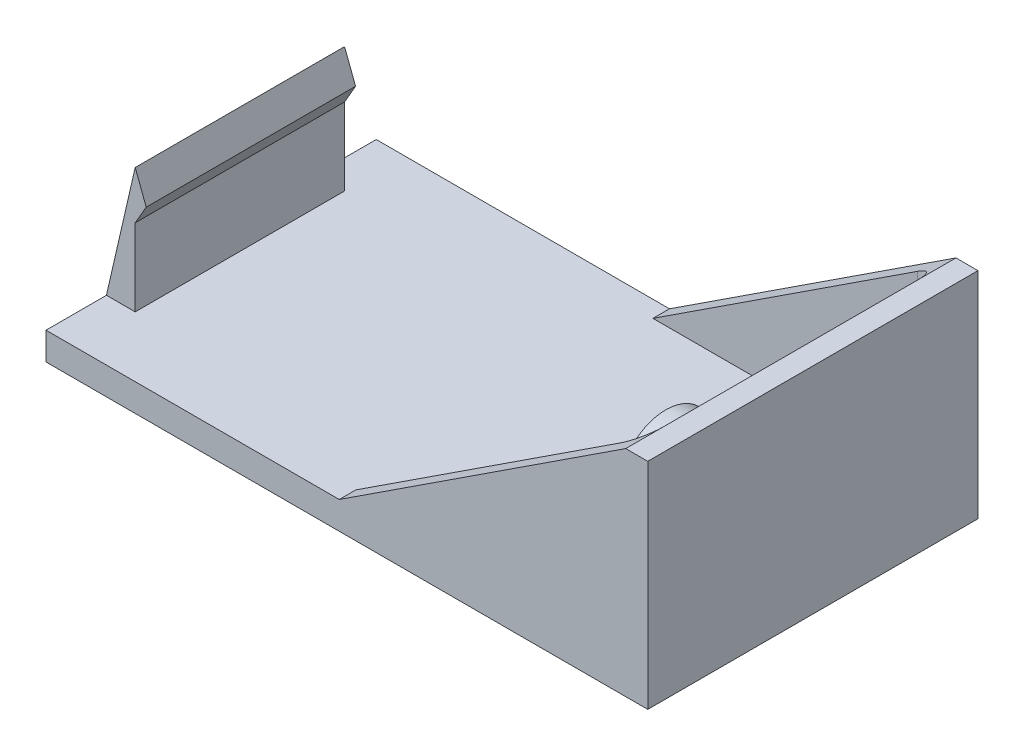
SolidWorks part; units mm, degrees
material "PUR"
ref_plane "Спереди" through (0, 0, 0) normal (0, 0, 1) x (1, 0, 0)
ref_plane "Сверху" through (0, 0, 0) normal (0, 1, 0) x (1, 0, 0)
ref_plane "Справа" through (0, 0, 0) normal (1, 0, 0) x (0, 0, -1)
sketch "Эскиз1" plane through (0, 0, 0) normal (0, 1, 0) x (1, 0, 0)
  line L1 (-27.305, 14.985) -> (27.305, 14.985)
  line L2 (-27.305, 14.985) -> (-27.305, -14.985)
  line L3 (-27.305, -14.985) -> (27.305, -14.985)
  line L4 (27.305, 14.985) -> (27.305, -14.985)
  line L5 (-27.305, 14.985) -> (27.305, -14.985) construction
  line L6 (-27.305, -14.985) -> (27.305, 14.985) construction
  point P0 (0, 0)
  dimension "D1" = 29.97
  dimension "D2" = 54.61
extrude "Бобышка-Вытянуть1" add sketch "Эскиз1" along normal blind 2.5
sketch "Эскиз2" plane through (0, 2.5, 0) normal (0, 1, 0) x (1, 0, 0)
  line L0 (27.305, -14.985) -> (-0.695, -14.985)
  line L1 (-27.305, -14.985) -> (27.305, -14.985) construction
  line L2 (-0.695, -14.985) -> (-0.695, -13.485)
  line L3 (-0.695, -13.485) -> (23.305, -13.485)
  line L4 (25.305, -11.485) -> (25.305, 11.485)
  line L5 (27.305, -14.985) -> (27.305, 14.985)
  line L6 (27.305, -14.985) -> (27.305, 14.985) construction
  line L7 (34.4496, 0) -> (-14.6404, 0) construction
  line L8 (27.305, 14.985) -> (-0.695, 14.985)
  line L9 (-0.695, 14.985) -> (-0.695, 13.485)
  line L10 (-0.695, 13.485) -> (23.305, 13.485)
  arc A0 (25.305, -11.485) -> (23.305, -13.485) centre (23.305, -11.485) cw
  arc A1 (25.305, 11.485) -> (23.305, 13.485) centre (23.305, 11.485) ccw
  point P17 (27.305, 0)
  point P22 (25.305, 0)
  dimension "D4" = 2
  dimension "D1" = 1.5
  dimension "D2" = 2
  dimension "D3" = 28
extrude "Бобышка-Вытянуть2" add sketch "Эскиз2" along normal blind 17
sketch "Эскиз3" plane through (0, 0, 14.985) normal (0, 0, 1) x (1, 0, 0)
  line L0 (-0.695, 2.5) -> (25.305, 19.5)
  line L1 (-0.695, 19.5) -> (27.305, 19.5) construction
  line L2 (25.305, 19.5) -> (-0.695, 19.5)
  line L3 (-0.695, 19.5) -> (-0.695, 2.5)
extrude "Вырез-Вытянуть1" cut sketch "Эскиз3" against normal through all
sketch "Эскиз8" plane through (0, 0, 0) normal (0, 0, 1) x (1, 0, 0)
  line L0 (-27.305, 2.5) -> (-24.695, 13.85)
  line L1 (-24.695, 13.85) -> (-23.695, 11.2321)
  line L2 (-23.695, 11.2321) -> (-24.695, 9.5)
  line L3 (-24.695, 9.5) -> (-24.695, 2.5)
  line L4 (-27.305, 2.5) -> (-0.695, 2.5) construction
  line L5 (-24.695, 2.5) -> (-27.305, 2.5)
  dimension "D2" = 49
  dimension "D3" = 7
  dimension "D4" = 1
  dimension "D5" = 2
extrude "Бобышка-Вытянуть4" add sketch "Эскиз8" along normal blind 9.5 and the other way blind 9.5
sketch "Эскиз10" plane through (25.305, 0, 0) normal (-1, 0, 0) x (0, 0, 1)
  line L0 (-18.4903, 11.48) -> (20.51, 11.48) construction
  line L1 (0, 0) -> (0, 20.3244) construction
  circle A0 centre (-6.35, 11.48) radius 3.75
  circle A1 centre (6.35, 11.48) radius 3.75
  dimension "D3" = 7.5
  dimension "D2" = 12.7
extrude "Бобышка-Вытянуть6" add sketch "Эскиз10" along normal blind 1
sketch "Эскиз11" plane through (24.305, 0, 0) normal (-1, 0, 0) x (0, 0, 1)
  circle A0 centre (-6.35, 11.48) radius 3
  circle A1 centre (-6.35, 11.48) radius 2
  dimension "D1" = 6
  dimension "D2" = 4
extrude "Бобышка-Вытянуть7" add sketch "Эскиз11" along normal blind 4
sketch "Эскиз12" plane through (24.305, 0, 0) normal (-1, 0, 0) x (0, 0, 1)
  circle A0 centre (6.35, 11.48) radius 4.25
  circle A1 centre (6.35, 11.48) radius 3.25
  dimension "D1" = 8.5
  dimension "D2" = 6.5
extrude "Бобышка-Вытянуть8" add sketch "Эскиз12" along normal blind 4
